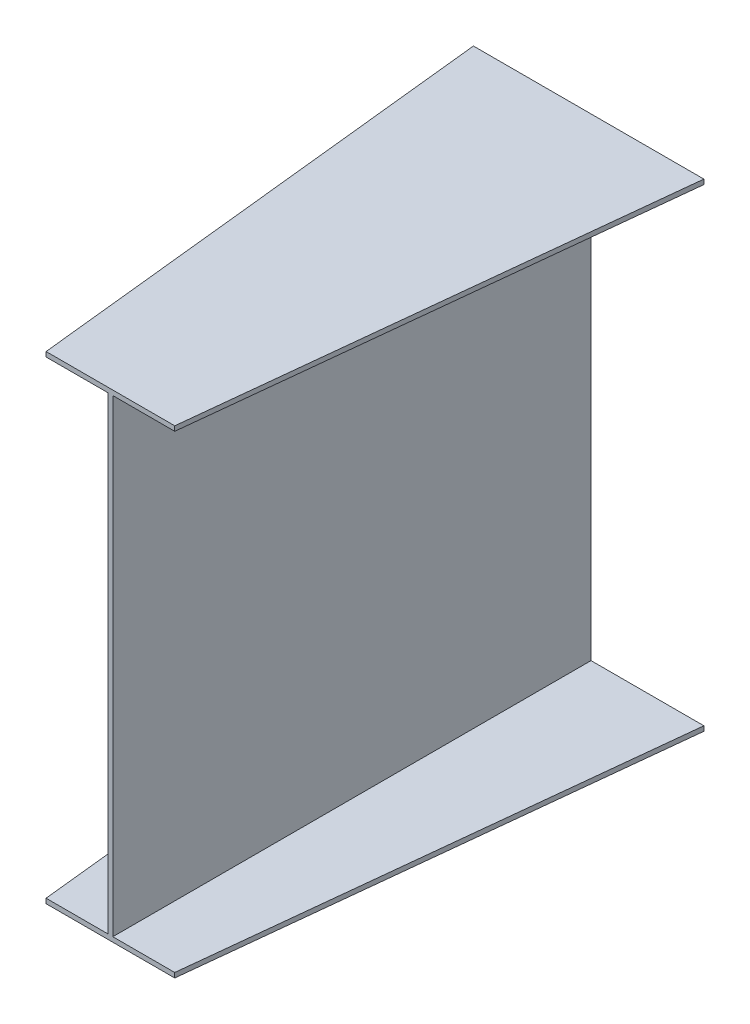
SolidWorks part; units mm, degrees
ref_plane "Front Plane" through (0, 0, 0) normal (0, 0, 1) x (1, 0, 0)
ref_plane "Top Plane" through (0, 0, 0) normal (0, 1, 0) x (1, 0, 0)
ref_plane "Right Plane" through (0, 0, 0) normal (1, 0, 0) x (0, 0, -1)
sketch "Sketch1" plane through (0, 0, 0) normal (0, 0, 1) x (1, 0, 0)
  line L0 (-236, -10) -> (246, -10)
  line L2 (0, 0) -> (0, 980)
  line L4 (10, 0) -> (10, 980)
  line L5 (-236, 980) -> (0, 980)
  line L6 (-236, 980) -> (-236, 990)
  line L7 (-236, 990) -> (246, 990)
  line L8 (246, 980) -> (246, 990)
  line L9 (246, -10) -> (246, 0)
  line L10 (-236, 0) -> (0, 0)
  line L11 (-236, -10) -> (-236, 0)
  line L12 (10, 980) -> (246, 980)
  line L13 (10, 0) -> (246, 0)
  dimension "D1" = 10
  dimension "D2" = 980
  dimension "D3" = 10
  dimension "D4" = 482
  dimension "D5" = 236
  dimension "D6" = 10
  dimension "D7" = 482
  dimension "D8" = 236
ref_plane "Plane1" through (0, 0, 1000) normal (0, 0, 1) x (1, 0, 0)
sketch "Sketch3" plane through (0, 0, 1000) normal (0, 0, 1) x (1, 0, 0)
  line L0 (-129.5, 990) -> (139.5, 990)
  line L2 (0, 0) -> (0, 980)
  line L4 (10, 0) -> (10, 980)
  line L5 (-129.5, 0) -> (0, 0)
  line L6 (-129.5, 0) -> (-129.5, -10)
  line L7 (-129.5, -10) -> (139.5, -10)
  line L8 (139.5, 0) -> (139.5, -10)
  line L9 (139.5, 990) -> (139.5, 980)
  line L10 (-129.5, 980) -> (0, 980)
  line L11 (-129.5, 990) -> (-129.5, 980)
  line L12 (10, 980) -> (139.5, 980)
  line L13 (10, 0) -> (139.5, 0)
  dimension "D1" = 10
  dimension "D2" = 269
  dimension "D3" = 129.5
  dimension "D4" = 10
  dimension "D5" = 129.5
  dimension "D6" = 269
loft "Loft3" add profiles "Sketch1", "Sketch3"
